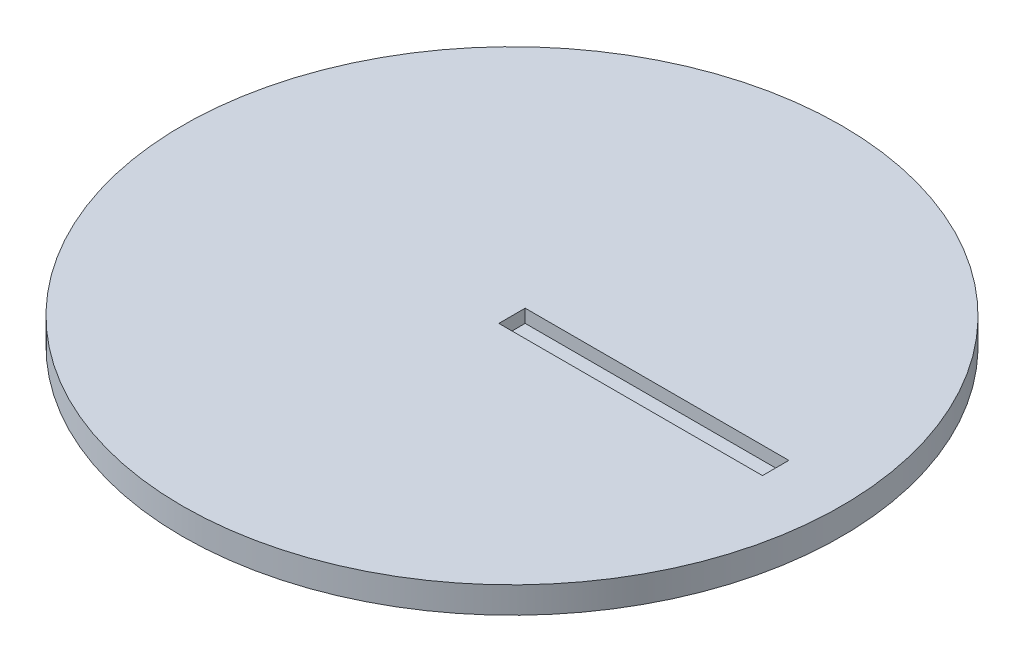
SolidWorks part; units mm, degrees
ref_plane "Front Plane" through (0, 0, 0) normal (0, 0, 1) x (1, 0, 0)
ref_plane "Top Plane" through (0, 0, 0) normal (0, 1, 0) x (1, 0, 0)
ref_plane "Right Plane" through (0, 0, 0) normal (1, 0, 0) x (0, 0, -1)
sketch "Sketch1" plane through (0, 0, 0) normal (0, 1, 0) x (1, 0, 0)
  circle A0 centre (0, 0) radius 25
  dimension "D1" = 50
extrude "Boss-Extrude1" add sketch "Sketch1" along normal blind 2 contours A0
sketch "Sketch2" plane through (0, 2, 0) normal (0, 1, 0) x (1, 0, 0)
  line L0 (0, 0) -> (20, 0)
  dimension "D1" = 20
extrude "Cut-Extrude-Thin1" cut sketch "Sketch2" against normal blind 1 and the other way through all thin thin type mid plane wall 2
